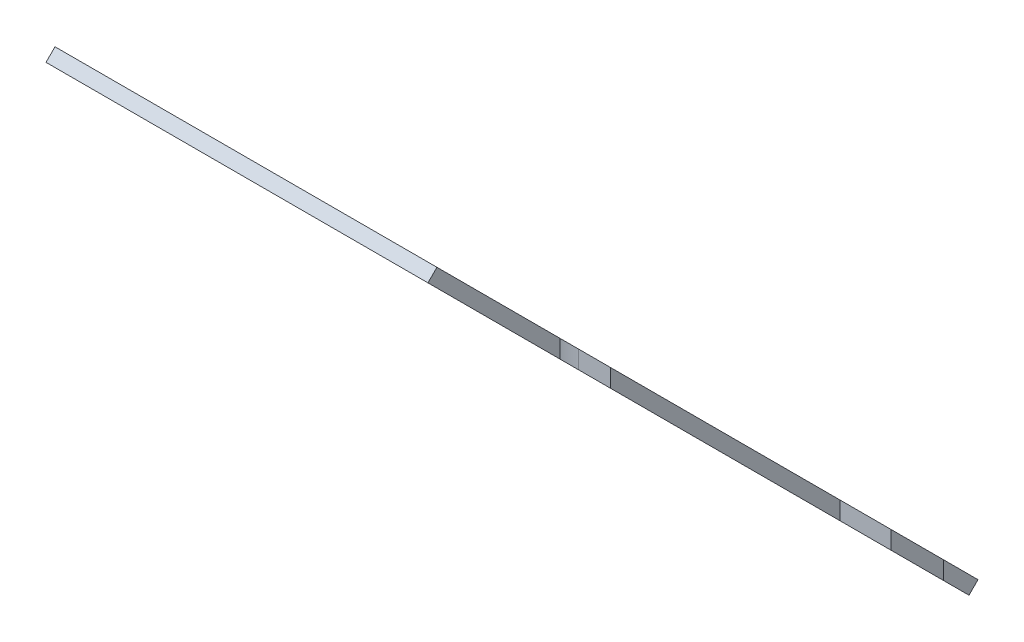
SolidWorks part; units mm, degrees
ref_plane "Plano frontal" through (0, 0, 0) normal (0, 0, 1) x (1, 0, 0)
ref_plane "Plano superior" through (0, 0, 0) normal (0, 1, 0) x (1, 0, 0)
ref_plane "Plano direito" through (0, 0, 0) normal (1, 0, 0) x (0, 0, -1)
sketch "Sketch3" plane through (0, 0, 0) normal (1, 0, 0) x (0, 0, -1)
  line L0 (-40199.9002, 3730.3647) -> (-40199.9002, 2810.9901) construction
  line L1 (-40199.9002, 12327.8571) -> (-40199.9002, -2672.1429) construction
  line L2 (-40199.9002, 2810.9901) -> (-41009.724, 3620.8139)
  line L3 (-41009.724, 3620.8139) -> (-40995.5819, 3634.9561)
  line L4 (-40995.5819, 3634.9561) -> (-40199.9002, 2839.2744)
  line L5 (-40199.9002, 2839.2744) -> (-40199.9002, 2810.9901)
  dimension "D1" = 20
  dimension "D2" = 45
extrude "Boss-Extrude1" add sketch "Sketch3" against normal blind 600 from surface at -22799.5611
sketch "Sketch4" plane through (0, 0, 0) normal (0, 1, 0) x (1, 0, 0)
  line L0 (-22799.5611, -40199.9002) -> (-22799.5611, -40995.5819) construction
  line L1 (-22799.5611, -40362.6002) -> (-23030.5611, -40362.6002)
  line L2 (-22799.5611, -40362.6002) -> (-22799.5611, -40282.6002)
  line L3 (-22799.5611, -40282.6002) -> (-23030.5611, -40282.6002)
  line L5 (-22850.5611, -40762.6002) -> (-22890.5611, -40762.6002) construction
  line L6 (-22799.5611, -40802.6002) -> (-22850.5611, -40802.6002)
  line L7 (-22799.5611, -40802.6002) -> (-22799.5611, -40722.6002)
  line L8 (-22799.5611, -40722.6002) -> (-22850.5611, -40722.6002)
  line L10 (-23030.5611, -40322.6002) -> (-23070.5611, -40322.6002) construction
  line L11 (-22850.5611, -40802.6002) -> (-22850.5611, -40722.6002) construction
  line L12 (-23030.5611, -40362.6002) -> (-23030.5611, -40282.6002) construction
  arc A4 (-23030.5611, -40282.6002) -> (-23030.5611, -40362.6002) centre (-23030.5611, -40322.6002) ccw
  arc A5 (-22850.5611, -40722.6002) -> (-22850.5611, -40802.6002) centre (-22850.5611, -40762.6002) ccw
extrude "Cut-Extrude1" cut sketch "Sketch4" against normal up to vertex from vertex
sketch "Sketch5" plane through (-23399.5611, 0, 0) normal (-1, 0, 0) x (0, 0, 1)
  line L0 (40199.9002, 2810.9901) -> (40043.6383, 2654.7282)
  line L1 (40043.6383, 2654.7282) -> (40043.6383, 2683.0125)
  line L2 (40043.6383, 2683.0125) -> (40199.9002, 2839.2744)
  line L3 (40199.9002, 2839.2744) -> (40199.9002, 2810.9901)
  line L4 (40043.6383, 2683.0125) -> (40057.7804, 2668.8703)
  line M8 (40199.9002, 2839.2744) -> (40199.9002, 2810.9901)
extrude "Boss-Extrude2" add sketch "Sketch5" against normal up to surface (498 mm away) contours L2 L4 L0 M8
sketch "Sketch6" plane through (0, -18680.3129, 18680.3129) normal (0, 0.7071, -0.7071) x (1, 0, 0)
  line L0 (-23159.5611, -30387.3045) -> (-23359.5611, -30387.3045) construction
  line L1 (-23159.5611, -30397.3045) -> (-23359.5611, -30397.3045)
  line L2 (-23159.5611, -30377.3045) -> (-23359.5611, -30377.3045)
  line L3 (-23359.5611, -30387.3045) -> (-23359.5611, -31189.3045) construction
  line L4 (-23349.5611, -30387.3045) -> (-23349.5611, -31189.3045)
  line L5 (-23369.5611, -30387.3045) -> (-23369.5611, -31189.3045)
  line L6 (-23359.5611, -31189.3045) -> (-22990.4389, -31189.3045) construction
  line L7 (-23359.5611, -31179.3045) -> (-22990.4389, -31179.3045)
  line L8 (-23359.5611, -31199.3045) -> (-22990.4389, -31199.3045)
  line L9 (-23399.5611, -31558.5561) -> (-23399.5611, -30212.3045) construction
  line L10 (-22901.5611, -30212.3045) -> (-23399.5611, -30212.3045) construction
  line L11 (-23159.5611, -30567.3045) -> (-23359.5611, -30567.3045) construction
  line L12 (-23159.5611, -30577.3045) -> (-23359.5611, -30577.3045)
  line L13 (-23159.5611, -30557.3045) -> (-23359.5611, -30557.3045)
  line L14 (-23359.5611, -31009.3045) -> (-22990.4389, -31009.3045) construction
  line L15 (-23359.5611, -30999.3045) -> (-22990.4389, -30999.3045)
  line L16 (-23359.5611, -31019.3045) -> (-22990.4389, -31019.3045)
  arc A0 (-23159.5611, -30397.3045) -> (-23159.5611, -30377.3045) centre (-23159.5611, -30387.3045) ccw
  arc A1 (-23359.5611, -30377.3045) -> (-23359.5611, -30397.3045) centre (-23359.5611, -30387.3045) ccw
  arc A2 (-23349.5611, -30387.3045) -> (-23369.5611, -30387.3045) centre (-23359.5611, -30387.3045) ccw
  arc A3 (-23369.5611, -31189.3045) -> (-23349.5611, -31189.3045) centre (-23359.5611, -31189.3045) ccw
  arc A4 (-23359.5611, -31179.3045) -> (-23359.5611, -31199.3045) centre (-23359.5611, -31189.3045) ccw
  arc A5 (-22990.4389, -31199.3045) -> (-22990.4389, -31179.3045) centre (-22990.4389, -31189.3045) ccw
  arc A6 (-23159.5611, -30577.3045) -> (-23159.5611, -30557.3045) centre (-23159.5611, -30567.3045) ccw
  arc A7 (-23359.5611, -30557.3045) -> (-23359.5611, -30577.3045) centre (-23359.5611, -30567.3045) ccw
  arc A8 (-23359.5611, -30999.3045) -> (-23359.5611, -31019.3045) centre (-23359.5611, -31009.3045) ccw
  arc A9 (-22990.4389, -31019.3045) -> (-22990.4389, -30999.3045) centre (-22990.4389, -31009.3045) ccw
  point P2 (-23259.5611, -30387.3045)
  point P7 (-23359.5611, -30788.3045)
  point P14 (-23175, -31189.3045)
  point P25 (-23159.5611, -31189.3045)
  point P26 (-23175, -31009.3045)
  point P29 (-23259.5611, -30567.3045)
  dimension "D1" = 10
  dimension "D3" = 40
  dimension "D4" = 175
  dimension "D5" = 802
  dimension "D6" = 2
  dimension "D7" = 2
extrude "Cut-Extrude2" cut sketch "Sketch6" against normal through all contours L8 A5 L7 L4 A3 | L7 A4 A3 L4 | L15 A9 L16 A8 | L13 A7 L12 A6 | L1 A1 L2 A0
sketch3d "3DSketch2"
  line L0 (-22990.4389, 3246.5766, 40607.2024) -> (-23359.5611, 3246.5766, 40607.2024) construction
  line L1 (-22990.4389, 3232.4344, 40621.3445) -> (-22990.4389, 3246.5766, 40607.2024) construction
  line L2 (-23359.5611, 2806.7561, 40167.382) -> (-23359.5611, 3246.5766, 40607.2024) construction
  line L3 (-23159.5611, 2806.7561, 40167.382) -> (-23359.5611, 2806.7561, 40167.382) construction
  line L4 (-23159.5611, 2792.614, 40181.5241) -> (-23159.5611, 2806.7561, 40167.382) construction
  line L5 (-23359.5611, 2792.614, 40181.5241) -> (-23359.5611, 2806.7561, 40167.382) construction
  line L6 (-23159.5611, 2806.7561, 40167.382) -> (-23354.5611, 2806.7561, 40167.382)
  line L7 (-23359.5611, 2810.2917, 40170.9175) -> (-23359.5611, 3243.041, 40603.6669)
  line L8 (-23354.5611, 3246.5766, 40607.2024) -> (-22990.4389, 3246.5766, 40607.2024)
  line L9 (-22990.4389, 3246.5766, 40607.2024) -> (-23159.5611, 2806.7561, 40167.382) construction
  arc A0 (-23354.5611, 2806.7561, 40167.382) -> (-23359.5611, 2810.2917, 40170.9175) centre (-23354.5611, 2810.2917, 40170.9175) ccw
  arc A1 (-23359.5611, 3243.041, 40603.6669) -> (-23354.5611, 3246.5766, 40607.2024) centre (-23354.5611, 3243.041, 40603.6669) ccw
  point P14 (-23359.5611, 2806.7561, 40167.382)
  point P16 (-23354.5611, 2813.8272, 40167.382)
  point P19 (-23359.5611, 3246.5766, 40607.2024)
  point P20 (-23354.5611, 3246.5766, 40600.1313)
  dimension "D1" = 5
